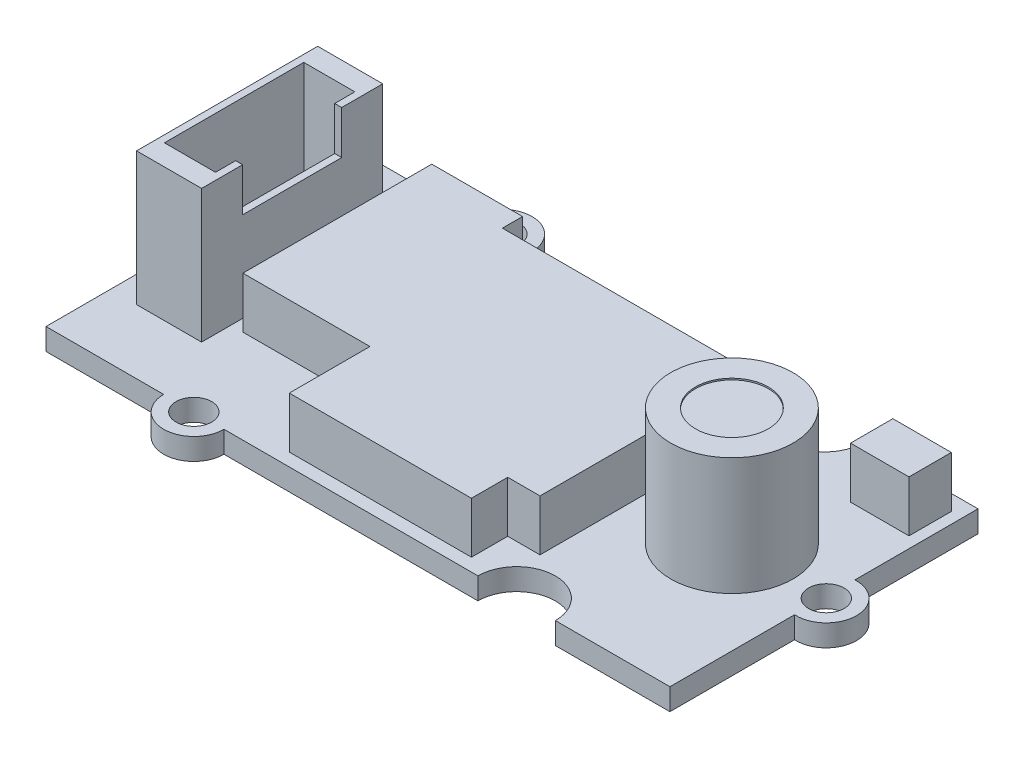
SolidWorks part; units mm, degrees
ref_plane "Front Plane" through (0, 0, 0) normal (0, 0, 1) x (1, 0, 0)
ref_plane "Top Plane" through (0, 0, 0) normal (0, 1, 0) x (1, 0, 0)
ref_plane "Right Plane" through (0, 0, 0) normal (1, 0, 0) x (0, 0, -1)
sketch "Sketch1" plane through (0, 0, 0) normal (0, 1, 0) x (1, 0, 0)
  line L0 (25.7386, -3.9909) -> (25.7386, -12.0437)
  line L1 (-14.5614, 7.8563) -> (-6.9614, 7.8563)
  line L2 (-14.5614, 7.8563) -> (-14.5614, 0.4561)
  line L3 (-14.5614, -12.0437) -> (-6.9614, -12.0437)
  line L4 (25.7386, 7.8563) -> (25.7386, -0.0964)
  line L5 (-14.5614, -4.5434) -> (-14.5614, -12.0437)
  line L6 (-3.0614, -12.0437) -> (13.3386, -12.0437)
  line L7 (-3.0614, 7.8563) -> (13.3386, 7.8563)
  line L8 (18.3386, 7.8563) -> (25.7386, 7.8563)
  line L9 (18.3386, -12.0437) -> (25.7386, -12.0437)
  arc A0 (25.7386, -3.9909) -> (25.7386, -0.0964) centre (25.8423, -2.0437) ccw
  circle A1 centre (25.8423, -2.0437) radius 1.15
  arc A2 (-14.5614, -4.5434) -> (-14.5614, 0.4561) centre (-14.5966, -2.0437) ccw
  arc A3 (13.3386, 7.8563) -> (18.3386, 7.8563) centre (15.8386, 7.8563) ccw
  arc A4 (18.3386, -12.0437) -> (13.3386, -12.0437) centre (15.8386, -12.0437) ccw
  arc A5 (-3.0614, 7.8563) -> (-6.9614, 7.8563) centre (-5.0114, 7.8563) ccw
  arc A6 (-6.9614, -12.0437) -> (-3.0614, -12.0437) centre (-5.0114, -12.0437) ccw
  circle A7 centre (-5.0114, -12.0437) radius 1.15
  circle A8 centre (-5.0114, 7.8563) radius 1.15
  point P25 (-14.5966, -2.0437)
  point P26 (25.7386, -2.0437)
  dimension "D3" = 3.9
  dimension "D4" = 2.3
  dimension "D5" = 5
  dimension "D6" = 5
  dimension "D7" = 5
  dimension "D10" = 3.9
  dimension "D11" = 3.9
  dimension "D14" = 2.3
  dimension "D15" = 2.3
  dimension "D1" = 40.3
  dimension "D2" = 19.9
  dimension "D8" = 12.4
  dimension "D9" = 12.4
  dimension "D12" = 11.5
  dimension "D13" = 11.5
extrude "Boss-Extrude1" add sketch "Sketch1" along normal blind 1.4
sketch "Sketch2" plane through (0, 1.4, 0) normal (0, 1, 0) x (1, 0, 0)
  line L0 (-14.5966, -2.0437) -> (25.8423, -2.0437) construction
  line L1 (15.7923, 7.4455) -> (15.7923, -11.4001) construction
  circle A0 centre (19.7423, -2.0437) radius 3.95
  arc A4 (25.7386, -3.9909) -> (25.7386, -0.0964) centre (25.8423, -2.0437) ccw construction
  point P11 (27.7923, -2.0437)
  dimension "D1" = 7.9
  dimension "D2" = 12
  dimension "D3" = 3.95
extrude "Boss-Extrude2" add sketch "Sketch2" along normal blind 9 from surface at -1.4 contours A0 starting at face at (5.7835, 0, 2.0812)
sketch "Sketch3" plane through (0, 1.4, 0) normal (0, 1, 0) x (1, 0, 0)
  line L1 (-12.8614, 3.8063) -> (-8.6614, 3.8063)
  line L2 (-12.8614, 3.8063) -> (-12.8614, -7.8937)
  line L3 (-12.8614, -7.8937) -> (-8.6614, -7.8937)
  line L4 (-8.6614, 3.8063) -> (-8.6614, -7.8937)
  line L5 (-14.5614, 7.8563) -> (-14.5614, 0.4561) construction
  arc A0 (-14.5614, -4.5434) -> (-14.5614, 0.4561) centre (-14.5966, -2.0437) ccw construction
  point P7 (-12.0966, -2.0437)
  point P8 (-8.6614, -2.0437)
  dimension "D1" = 4.2
  dimension "D2" = 11.7
  dimension "D3" = 0
  dimension "D4" = 5.9
extrude "Boss-Extrude4" add sketch "Sketch3" along normal blind 8.6 contours L4 L3 L2 L1
sketch "Sketch4" plane through (0, 10, 0) normal (0, 1, 0) x (1, 0, 0)
  line L1 (-12.4114, 2.4563) -> (-9.1114, 2.4563)
  line L2 (-12.4114, 2.4563) -> (-12.4114, -6.5437)
  line L3 (-12.4114, -6.5437) -> (-9.1114, -6.5437)
  line L4 (-9.1114, 2.4563) -> (-9.1114, -6.5437)
  line L5 (-12.8614, 3.8063) -> (-8.6614, 3.8063) construction
  line L6 (-8.6614, 3.8063) -> (-8.6614, -7.8937) construction
  point P4 (-10.7614, 2.4563)
  point P7 (-10.7614, 3.8063)
  point P8 (-9.1114, -2.0437)
  point P11 (-8.6614, -2.0437)
  dimension "D1" = 9
  dimension "D2" = 3.3
  dimension "D3" = 0
  dimension "D4" = 0
extrude "Cut-Extrude1" cut sketch "Sketch4" against normal blind 7
sketch "Sketch5" plane through (0, 10, 0) normal (0, 1, 0) x (1, 0, 0)
  line L0 (-9.1114, -6.5437) -> (-9.1114, 2.4563) construction
  line L1 (-9.1114, 1.1563) -> (-8.6614, 1.1563)
  line L2 (-9.1114, 1.1563) -> (-9.1114, -5.2437)
  line L3 (-9.1114, -5.2437) -> (-8.6614, -5.2437)
  line L4 (-8.6614, 1.1563) -> (-8.6614, -5.2437)
  line L5 (-8.6614, 3.8063) -> (-8.6614, -7.8937) construction
  line L6 (-12.8614, 3.8063) -> (-12.8614, -7.8937) construction
  point P8 (-12.8614, -2.0437)
  point P11 (-9.1114, -2.0437)
  dimension "D1" = 6.4
  dimension "D2" = 0
extrude "Cut-Extrude2" cut sketch "Sketch5" against normal blind 2.8
sketch "Sketch6" plane through (0, 1.4, 0) normal (0, 1, 0) x (1, 0, 0)
  line L0 (-7.8848, 6.1984) -> (-2.0239, 6.1984)
  line L5 (-2.0239, 6.1984) -> (-2.0239, 4.896)
  line L6 (-2.0239, 4.896) -> (17.2518, 4.896)
  line L7 (17.2518, 4.896) -> (17.2518, 1.9872)
  line L8 (17.2518, 1.9872) -> (14.1695, 1.9872)
  line L9 (14.1695, 1.9872) -> (14.1695, -8.8663)
  line L10 (14.1695, -8.8663) -> (12.0856, -8.8663)
  line L11 (12.0856, -8.8663) -> (12.0856, -11.2106)
  line L12 (12.0856, -11.2106) -> (0.3204, -11.2106)
  line L13 (0.3204, -11.2106) -> (0.3204, -6.0009)
  line L14 (0.3204, -6.0009) -> (-7.8848, -6.0009)
  line L15 (-7.8848, -6.0009) -> (-7.8848, 6.1984)
  line L17 (21.2459, 6.8496) -> (25.0229, 6.8496)
  line L18 (21.2459, 6.8496) -> (21.2459, 4.1145)
  line L19 (21.2459, 4.1145) -> (25.0229, 4.1145)
  line L20 (25.0229, 6.8496) -> (25.0229, 4.1145)
extrude "Boss-Extrude6" add sketch "Sketch6" along normal blind 3.3
sketch "Sketch7" plane through (0, 0, 0) normal (0, -1, 0) x (1, 0, 0)
  line L0 (25.7386, 12.0437) -> (25.7386, 3.9909) construction
  line L1 (17.8386, 4.2937) -> (22.3386, 4.2937)
  line L2 (17.8386, 4.2937) -> (17.8386, -0.2063)
  line L3 (17.8386, -0.2063) -> (22.3386, -0.2063)
  line L4 (22.3386, 4.2937) -> (22.3386, -0.2063)
  circle A0 centre (25.8423, 2.0437) radius 1.15 construction
  point P4 (22.3386, 2.0437)
  dimension "D1" = 4.5
  dimension "D2" = 0
  dimension "D3" = 3.4
extrude "Boss-Extrude7" add sketch "Sketch7" along normal blind 1.1
sketch "Sketch8" plane through (0, 9, 0) normal (0, 1, 0) x (1, 0, 0)
  circle A0 centre (19.7423, -2.0437) radius 2.35
  dimension "D1" = 4.7
extrude "Cut-Extrude3" cut sketch "Sketch8" against normal blind 0.1
